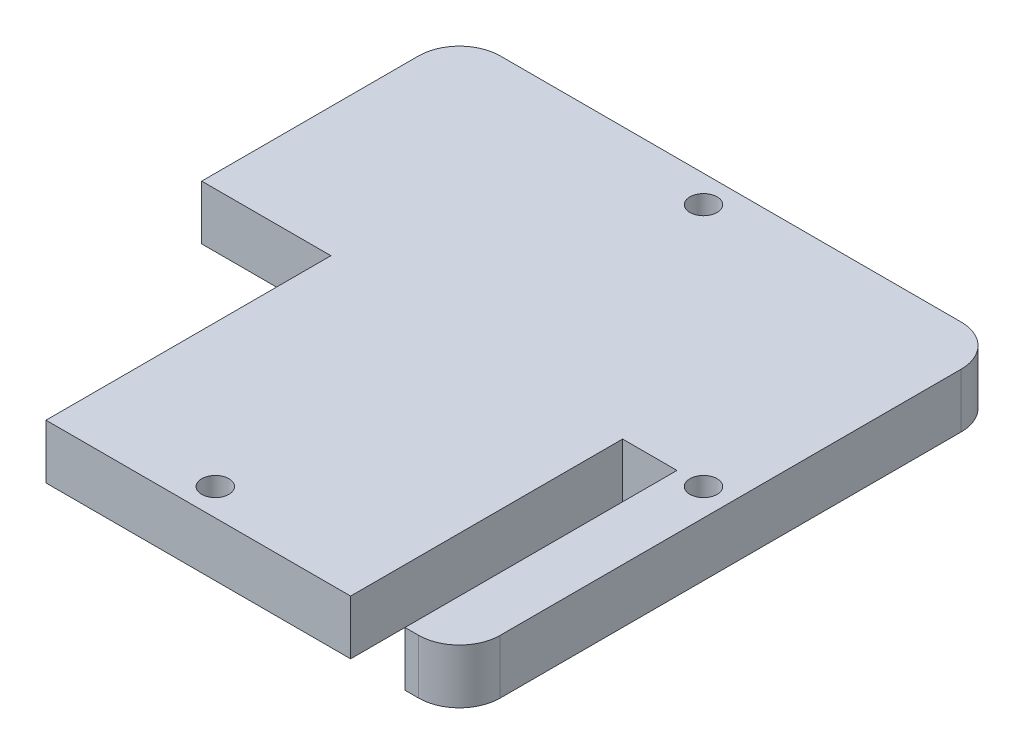
SolidWorks part; units mm, degrees
ref_plane "Alzado" through (0, 0, 0) normal (0, 0, 1) x (1, 0, 0)
ref_plane "Planta" through (0, 0, 0) normal (0, 1, 0) x (1, 0, 0)
ref_plane "Vista lateral" through (0, 0, 0) normal (1, 0, 0) x (0, 0, -1)
sketch "Croquis1" plane through (0, 0, 0) normal (0, 1, 0) x (1, 0, 0)
  line L15 (-19.95, 19.95) -> (19.95, 19.95)
  line L16 (-19.95, 19.95) -> (-19.95, -19.95)
  line L17 (-19.95, -19.95) -> (19.95, -19.95)
  line L18 (19.95, 19.95) -> (19.95, -19.95)
  line L19 (-15.95, 15.95) -> (15.95, 15.95)
  line L20 (-15.95, 15.95) -> (-15.95, -15.95)
  line L21 (-15.95, -15.95) -> (15.95, -15.95)
  line L22 (15.95, 15.95) -> (15.95, -15.95)
  point P12 (0, 15.95)
  point P13 (15.95, 0)
  dimension "D1" = 39.9
  dimension "D2" = 39.9
  dimension "D3" = 4
  dimension "D4" = 4
  dimension "D5" = 4
  dimension "D6" = 4
extrude "Saliente-Extruir1" add sketch "Croquis1" along normal mid plane 4
sketch "Croquis7" plane through (0, 0, 0) normal (0, 1, 0) x (1, 0, 0)
  line L0 (19.95, 19.95) -> (19.95, -19.95) construction
  line L1 (15.95, -19.95) -> (11.95, -19.95)
  line L2 (15.95, -19.95) -> (15.95, 0.05)
  line L3 (15.95, 0.05) -> (11.95, 0.05)
  line L4 (11.95, -19.95) -> (11.95, 0.05)
  line L5 (-19.95, -19.95) -> (19.95, -19.95) construction
  line L6 (0, -2.2) -> (0, 2.2) construction
  line L7 (-11.95, -19.95) -> (-11.95, 0.05)
  line L8 (-15.95, 0.05) -> (-11.95, 0.05)
  line L9 (-15.95, -19.95) -> (-15.95, 0.05)
  line L10 (-15.95, -19.95) -> (-11.95, -19.95)
  dimension "D1" = 20
  dimension "D2" = 4
  dimension "D3" = 4
extrude "Cortar-Extruir3" cut sketch "Croquis7" against normal through all both and the other way through all
sketch "Croquis9" plane through (0, -2, 0) normal (0, -1, 0) x (1, 0, 0)
  line L0 (-19.95, -19.95) -> (-19.95, 19.95) construction
  line L1 (-19.95, 19.95) -> (-15.95, 19.95) construction
  line L2 (19.95, -19.95) -> (19.95, 19.95) construction
  line L3 (-19.95, -19.95) -> (19.95, -19.95) construction
  circle A0 centre (0, 17.95) radius 1
  circle A1 centre (-17.95, 0) radius 1
  circle A2 centre (0, -17.95) radius 1
  circle A3 centre (17.95, 0) radius 1
  dimension "D1" = 2
  dimension "D2" = 2
  dimension "D3" = 2
  dimension "D4" = 2
  dimension "D5" = 2
extrude "Cortar-Extruir4" cut sketch "Croquis9" against normal through all both and the other way through all
fillet "Redondeo8" radius 3 4 edges at (19.95, 0, -19.95) (-19.95, 0, -19.95) (-19.95, 0, 19.95) (19.95, 0, 19.95)
sketch "Croquis10" plane through (0, 2, 0) normal (0, 1, 0) x (1, 0, 0)
  line L0 (-19.95, 16.95) -> (-19.95, -16.95) construction
  line L1 (-19.95, 1) -> (-10.45, 1)
  line L2 (-19.95, 1) -> (-19.95, -19.95)
  line L3 (-19.95, -19.95) -> (-10.45, -19.95)
  line L4 (-10.45, 1) -> (-10.45, -19.95)
  line L5 (-11.95, -19.95) -> (11.95, -19.95) construction
  line L6 (-11.95, -19.95) -> (-11.95, 0.05) construction
  line L8 (-13.95, 0.05) -> (-13.95, 1) construction
  line L9 (-11.95, 0.05) -> (-15.95, 0.05) construction
  circle A0 centre (-17.95, 0) radius 1 construction
  dimension "D1" = 1.5
extrude "Cortar-Extruir5" cut sketch "Croquis10" against normal through all both and the other way through all
